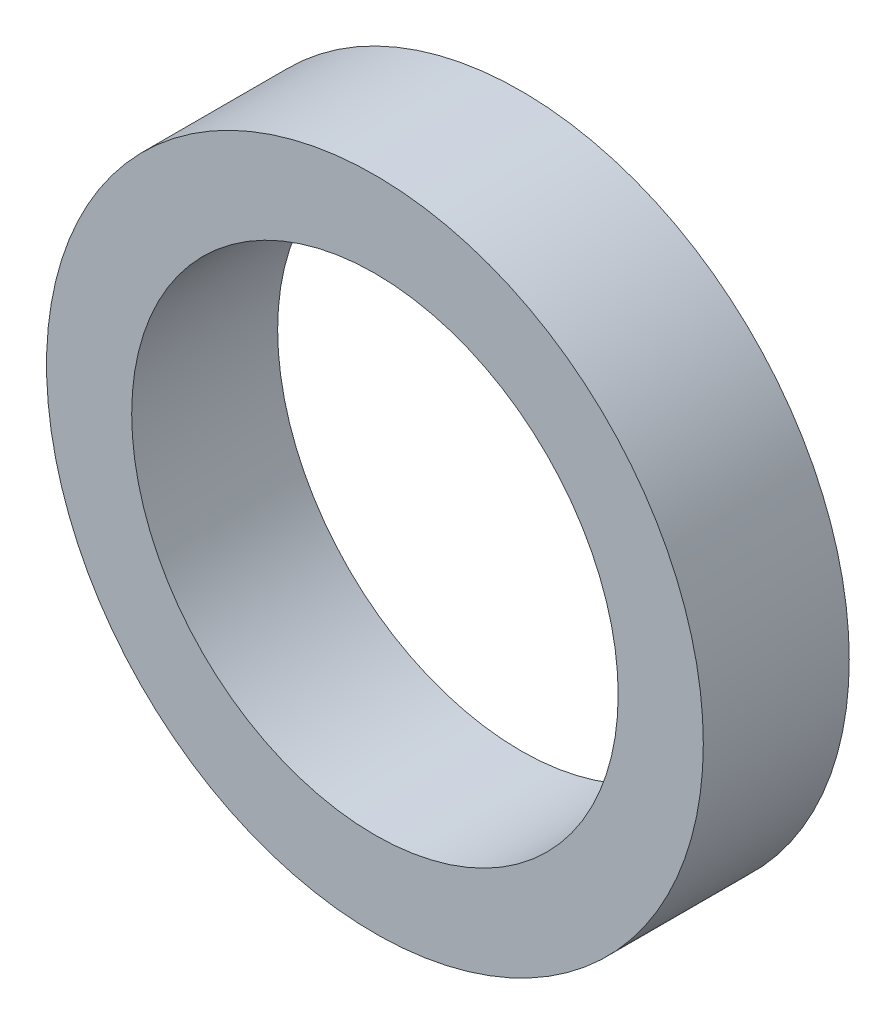
SolidWorks part; units mm, degrees
ref_plane "Front Plane" through (0, 0, 0) normal (0, 0, 1) x (1, 0, 0)
ref_plane "Top Plane" through (0, 0, 0) normal (0, 1, 0) x (1, 0, 0)
ref_plane "Right Plane" through (0, 0, 0) normal (1, 0, 0) x (0, 0, -1)
sketch "Sketch1" plane through (0, 0, 0) normal (0, 0, 1) x (1, 0, 0)
  circle A0 centre (0, 0) radius 13.5
  dimension "D1" = 27
extrude "Boss-Extrude1" add sketch "Sketch1" along normal blind 6
sketch "Sketch2" plane through (0, 0, 0) normal (0, 0, -1) x (-1, 0, 0)
  circle A0 centre (0, 0) radius 10
  dimension "D1" = 20
extrude "Cut-Extrude1" cut sketch "Sketch2" against normal through all
